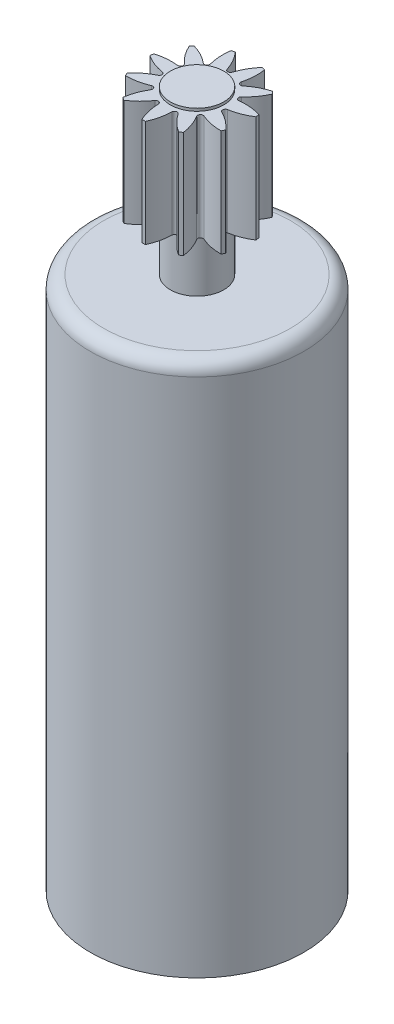
SolidWorks part; units mm, degrees
ref_plane "Front Plane" through (0, 0, 0) normal (0, 0, 1) x (1, 0, 0)
ref_plane "Top Plane" through (0, 0, 0) normal (0, 1, 0) x (1, 0, 0)
ref_plane "Right Plane" through (0, 0, 0) normal (1, 0, 0) x (0, 0, -1)
sketch "Sketch1" plane through (0, 0, 0) normal (0, 0, 1) x (1, 0, 0)
  line L0 (0, 0) -> (0, 26.1)
  line L1 (0, 0) -> (4, 0)
  line L2 (4, 0) -> (4, 19.5)
  line L3 (3.5, 20) -> (1, 20)
  line L4 (1, 20) -> (1, 22)
  line L5 (1, 22) -> (2, 22)
  line L6 (2, 22) -> (2, 26)
  line L7 (0, 26.1) -> (1, 26.1)
  line L8 (1, 26.1) -> (1, 26)
  line L9 (1, 26) -> (2, 26)
  arc A0 (4, 19.5) -> (3.5, 20) centre (3.5, 19.5) ccw
  point P13 (4, 20)
  dimension "D8" = 0.5
  dimension "D1" = 26.1
  dimension "D2" = 2
  dimension "D3" = 4
  dimension "D4" = 4
  dimension "D5" = 3
  dimension "D6" = 0.1
  dimension "D7" = 1
revolve "Revolve1" add sketch "Sketch1" angle 360 about L0
sketch "Sketch2" plane through (0, 26, 0) normal (0, 1, 0) x (1, 0, 0)
  line L0 (0, 0) -> (0, 2) construction
  circle A0 centre (0, 0) radius 2 construction
  arc A1 (-0.5, 1.9365) -> (0.5, 1.9365) centre (0, 0) cw
  arc A2 (0.5, 1.9365) -> (0.0953, 1.2198) centre (2.002, 0.6158) ccw
  arc A3 (0.0953, 1.2198) -> (-0.0953, 1.2198) centre (0, 1.25) cw
  arc A4 (-0.5, 1.9365) -> (-0.0953, 1.2198) centre (-2.002, 0.6158) cw
  dimension "D2" = 2
  dimension "D3" = 0.1
  dimension "D1" = 1
  dimension "D4" = 0.75
extrude "Cut-Extrude1" cut sketch "Sketch2" against normal up to surface (4 mm away) up to face at (0, 22, -2)
pattern_circular "CirPattern1" count 11 over 360 about axis through (0, 0, 0) along (0, 1, 0) of "Cut-Extrude1"
